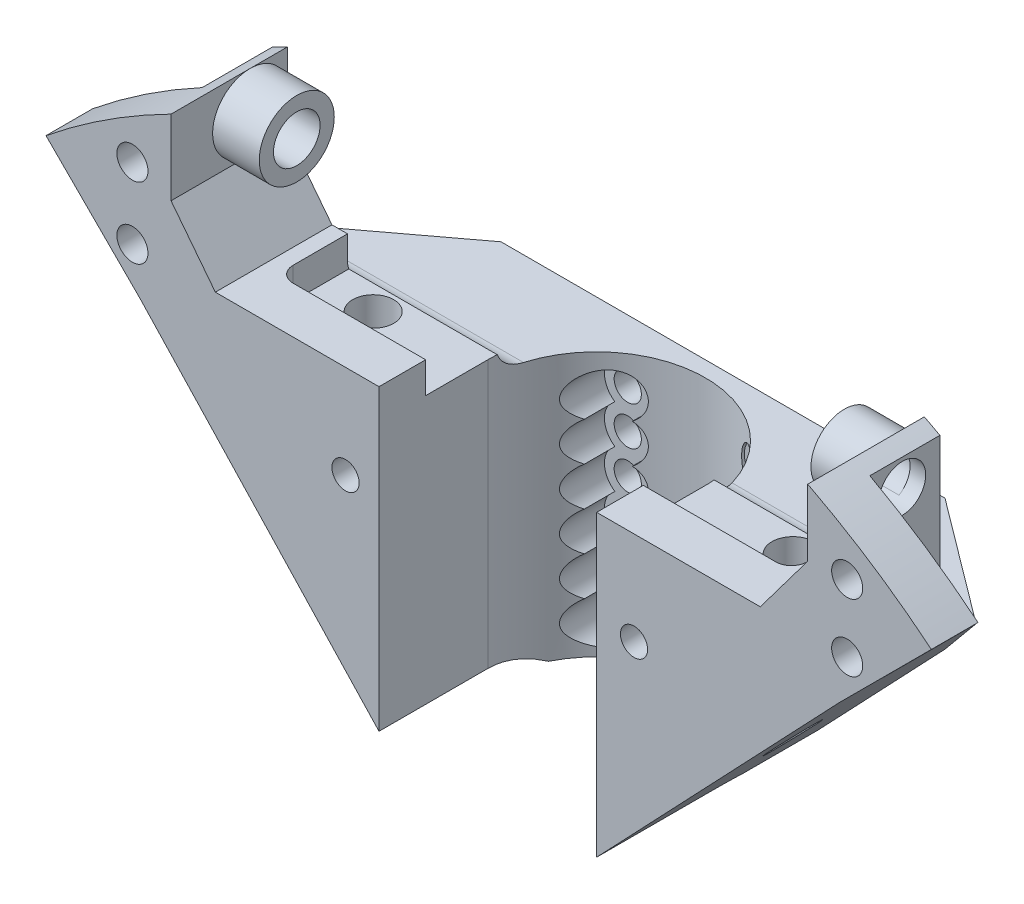
SolidWorks part; units mm, degrees
ref_plane "Front Plane" through (0, 0, 0) normal (0, 0, 1) x (1, 0, 0)
ref_plane "Top Plane" through (0, 0, 0) normal (0, 1, 0) x (1, 0, 0)
ref_plane "Right Plane" through (0, 0, 0) normal (1, 0, 0) x (0, 0, -1)
sketch "Model" plane through (0, 0, 0) normal (0, 0, 1) x (1, 0, 0)
  line L0 (265.571, 46.228) -> (275.731, 56.388)
  line L1 (387.491, 140.716) -> (398.667, 148.844)
  line L2 (349.899, 55.88) -> (359.551, 46.228)
  line L3 (379.871, 94.488) -> (394.603, 85.344)
  line L4 (349.899, 55.88) -> (379.871, 94.488)
  line L5 (358.027, 180.34) -> (369.711, 192.024)
  line L6 (239.155, 141.732) -> (268.111, 180.34)
  line L7 (245.759, 94.488) -> (275.731, 56.388)
  line L8 (227.471, 150.368) -> (239.155, 141.732)
  line L9 (231.027, 84.836) -> (245.759, 94.488)
  line L10 (272.0625, 193.262) -> (272.0625, 202.914)
  line L11 (255.919, 192.532) -> (268.111, 180.34)
  line L12 (353.963, 194.056) -> (353.963, 202.184)
  line L13 (277.763, 185.928) -> (347.867, 185.928)
  line L14 (272.0625, 193.262) -> (277.763, 185.928)
  line L15 (347.867, 185.928) -> (353.963, 194.056)
  line L16 (358.027, 180.34) -> (387.491, 140.716)
  circle A0 centre (288.285, 50.903) radius 0.35
  circle A1 centre (288.285, 47.903) radius 0.35
  circle A2 centre (313.04, 43.867) radius 0.35
  circle A3 centre (313.04, 40.867) radius 0.35
  circle A4 centre (338.328, 47.752) radius 0.35
  circle A5 centre (338.328, 50.752) radius 0.35
  circle A6 centre (388.747, 117.475) radius 0.35
  circle A7 centre (385.747, 117.475) radius 0.35
  circle A8 centre (235.939, 117.475) radius 0.35
  circle A9 centre (238.939, 117.475) radius 0.35
  circle A10 centre (282.458, 118.999) radius 0.35
  circle A11 centre (282.458, 115.999) radius 0.35
  circle A12 centre (289.914, 95.9) radius 0.35
  circle A13 centre (292.914, 95.9) radius 0.35
  circle A14 centre (312.938, 85.446) radius 0.35
  circle A15 centre (312.938, 88.446) radius 0.35
  circle A16 centre (332.915, 95.885) radius 0.35
  circle A17 centre (335.915, 95.885) radius 0.35
  circle A18 centre (343.423, 119.026) radius 0.35
  circle A19 centre (343.423, 116.026) radius 0.35
  circle A20 centre (335.94, 139.075) radius 0.35
  circle A21 centre (332.94, 139.075) radius 0.35
  circle A22 centre (292.916, 138.918) radius 0.35
  circle A23 centre (289.916, 138.918) radius 0.35
  circle A24 centre (337.942, 181.002) radius 0.35
  circle A25 centre (337.942, 178.002) radius 0.35
  circle A26 centre (313.05, 149.379) radius 0.35
  circle A27 centre (313.05, 146.379) radius 0.35
  circle A28 centre (313.558, 171.817) radius 0.35
  circle A29 centre (313.558, 168.817) radius 0.35
  circle A30 centre (286.004, 181.078) radius 0.35
  circle A31 centre (286.004, 178.078) radius 0.35
  circle A32 centre (326.3085, 83.1484) radius 0.55
  circle A33 centre (328.2542, 81.5157) radius 0.55
  circle A34 centre (330.2, 79.883) radius 0.55
  circle A35 centre (332.1457, 78.2503) radius 0.55
  circle A36 centre (334.0915, 76.6176) radius 0.55
  circle A37 centre (336.0373, 74.985) radius 0.55
  circle A38 centre (337.983, 73.3523) radius 0.55
  circle A39 centre (339.9288, 71.7196) radius 0.55
  circle A40 centre (265.571, 46.228) radius 0.125
  circle A41 centre (275.731, 56.388) radius 0.125
  circle A42 centre (387.491, 140.716) radius 0.125
  circle A43 centre (398.667, 148.844) radius 0.125
  circle A44 centre (349.899, 55.88) radius 0.125
  circle A45 centre (359.551, 46.228) radius 0.125
  circle A46 centre (379.871, 94.488) radius 0.125
  circle A47 centre (394.603, 85.344) radius 0.125
  circle A48 centre (349.899, 55.88) radius 0.125
  circle A49 centre (379.871, 94.488) radius 0.125
  circle A50 centre (358.027, 180.34) radius 0.125
  circle A51 centre (369.711, 192.024) radius 0.125
  circle A52 centre (239.155, 141.732) radius 0.125
  circle A53 centre (268.111, 180.34) radius 0.125
  circle A54 centre (245.759, 94.488) radius 0.125
  circle A55 centre (275.731, 56.388) radius 0.125
  circle A56 centre (227.471, 150.368) radius 0.125
  circle A57 centre (239.155, 141.732) radius 0.125
  circle A58 centre (231.027, 84.836) radius 0.125
  circle A59 centre (245.759, 94.488) radius 0.125
  circle A60 centre (272.0625, 193.262) radius 0.2
  circle A61 centre (272.0625, 202.914) radius 0.2
  circle A62 centre (255.919, 192.532) radius 0.125
  circle A63 centre (268.111, 180.34) radius 0.125
  circle A64 centre (353.963, 194.056) radius 0.2
  circle A65 centre (353.963, 202.184) radius 0.2
  circle A66 centre (277.763, 185.928) radius 0.2
  circle A67 centre (347.867, 185.928) radius 0.2
  circle A68 centre (272.0625, 193.262) radius 0.2
  circle A69 centre (277.763, 185.928) radius 0.2
  circle A70 centre (347.867, 185.928) radius 0.2
  circle A71 centre (353.963, 194.056) radius 0.2
  circle A72 centre (358.027, 180.34) radius 0.125
  circle A73 centre (387.491, 140.716) radius 0.125
  circle A74 centre (312.547, 118.364) radius 10
  circle A75 centre (322.547, 118.364) radius 0.125
  circle A76 centre (302.547, 118.364) radius 0.125
  arc A77 (272.0625, 202.914) -> (353.9423, 202.6508) centre (312.7448, 122.6335) ccw
  circle A78 centre (353.9423, 202.6508) radius 0.2
  circle A79 centre (272.0621, 202.9138) radius 0.2
  circle A80 centre (341.009, 84.201) radius 2.5
  circle A81 centre (227.2882, 125.7761) radius 2
  circle A82 centre (227.1612, 118.1561) radius 2
  circle A83 centre (227.711, 110.744) radius 2
  circle A84 centre (227.8719, 133.9959) radius 2
  circle A85 centre (278.0556, 43.4621) radius 2
  circle A86 centre (295.1546, 37.9063) radius 2
  circle A87 centre (330.9154, 37.9063) radius 2
  circle A88 centre (348.0144, 43.4621) radius 2
  circle A89 centre (398.1981, 110.0581) radius 2
  circle A90 centre (399.035, 122.027) radius 2
  circle A91 centre (398.1981, 133.9959) radius 2
  circle A92 centre (395.859, 97.917) radius 2
  circle A93 centre (228.854, 102.997) radius 2
  circle A94 centre (231.013, 94.996) radius 2
  circle A95 centre (271.145, 46.736) radius 2
  circle A96 centre (286.258, 40.386) radius 2
  circle A97 centre (303.911, 36.322) radius 2
  circle A98 centre (322.072, 36.322) radius 2
  circle A99 centre (339.344, 40.386) radius 2
  circle A100 centre (354.076, 47.244) radius 2
  circle A101 centre (393.319, 90.043) radius 2
  circle A102 centre (396.367, 143.256) radius 2
  circle A103 centre (229.235, 144.018) radius 2
  circle A104 centre (313.035, 36.027) radius 2
  circle A105 centre (284.099, 152.527) radius 2.5
  circle A106 centre (272.288, 134.493) radius 2.5
  circle A107 centre (343.027, 152.273) radius 2.5
  circle A108 centre (258.6243, 93.2791) radius 2
  circle A109 centre (324.88, 146.685) radius 2
  circle A110 centre (299.988, 146.685) radius 2
  circle A111 centre (323.864, 177.165) radius 2
  circle A112 centre (301.512, 177.165) radius 2
  circle A113 centre (272.81, 98.425) radius 2.5
  circle A114 centre (352.806, 135.763) radius 2.5
  circle A115 centre (285.6744, 84.5154) radius 2.5
  circle A116 centre (252.871, 143.764) radius 2
  circle A117 centre (355.487, 167.64) radius 2
  circle A118 centre (277.4203, 69.9111) radius 2
  circle A119 centre (348.375, 69.596) radius 2
  circle A120 centre (373.775, 142.748) radius 2
  circle A121 centre (367.171, 93.472) radius 2
  circle A122 centre (270.651, 168.148) radius 2
  circle A123 centre (267.095, 185.928) radius 2
  circle A124 centre (359.043, 185.928) radius 2
  circle A125 centre (352.185, 97.917) radius 2.5
  circle A126 centre (324.88, 152.781) radius 2.5
  circle A127 centre (299.988, 152.781) radius 2.5
  circle A128 centre (323.864, 182.245) radius 2
  circle A129 centre (312.815, 96.52) radius 2
  circle A130 centre (312.815, 101.6) radius 2
  circle A131 centre (359.043, 194.564) radius 2
  circle A132 centre (301.512, 182.245) radius 2
  circle A133 centre (267.095, 195.072) radius 2
  circle A134 centre (312.547, 154.813) radius 1.75
sketch "Sketch2" plane through (0, 0, 0) normal (0, 0, 1) x (1, 0, 0)
  line L0 (369.8693, 192.1806) -> (358.027, 180.34)
  line L1 (255.978, 192.4729) -> (268.111, 180.34)
  line L2 (268.111, 180.34) -> (300.315, 145.928)
  line L3 (353.963, 202.6401) -> (353.963, 194.056)
  line L4 (353.963, 194.056) -> (347.867, 185.928)
  line L5 (347.867, 185.928) -> (277.763, 185.928)
  line L6 (277.763, 185.928) -> (272.0625, 193.262)
  line L7 (272.0625, 193.262) -> (272.0625, 202.914)
  line L8 (300.315, 145.928) -> (325.315, 145.928)
  line L9 (325.315, 145.928) -> (358.027, 180.34)
  line L10 (312.815, 185.928) -> (312.815, 145.928) construction
  arc A0 (272.0625, 202.914) -> (255.978, 192.4729) centre (312.7448, 122.6335) ccw
  arc A1 (272.0625, 202.914) -> (353.9423, 202.6508) centre (312.7448, 122.6335) ccw construction
  arc A3 (369.8693, 192.1806) -> (353.963, 202.6401) centre (312.7448, 122.6335) ccw
  point P11 (0, 0)
  point P13 (0, 0)
  point P31 (369.8693, 192.1806)
  point P32 (0, 0)
  point P33 (369.711, 192.024)
  point P34 (0, 0)
  point P35 (0, 0)
  point P36 (0, 0)
  dimension "D1" = 40
  dimension "D2" = 25
extrude "Boss-Extrude1" add sketch "Sketch2" along normal blind 30
sketch "Sketch3" plane through (0, 185.928, 0) normal (0, 1, 0) x (1, 0, 0)
  line L1 (312.815, -16) -> (312.815, -30) construction
  line L2 (347.867, -30) -> (277.763, -30) construction
  line L3 (326.815, -16) -> (326.815, -30)
  line L4 (326.815, -30) -> (298.815, -30)
  line L5 (298.815, -30) -> (298.815, -16)
  arc A0 (326.815, -16) -> (298.815, -16) centre (312.815, -16) ccw
  dimension "D1" = 28
  dimension "D2" = 14
extrude "Cut-Extrude1" cut sketch "Sketch3" against normal through all
sketch "Sketch4" plane through (0, 0, 0) normal (0, 0, -1) x (-1, 0, 0)
  circle A0 centre (-359.043, 194.564) radius 2
  circle A1 centre (-359.043, 185.928) radius 2
  circle A6 centre (-267.095, 185.928) radius 2
  circle A7 centre (-267.095, 195.072) radius 2
extrude "Cut-Extrude2" cut sketch "Sketch4" against normal through all
sketch "Sketch5" plane through (0, 185.928, 0) normal (0, 1, 0) x (1, 0, 0)
  line L0 (298.815, -30) -> (277.763, -30) construction
  line L1 (281.763, -10) -> (343.867, -10)
  line L2 (279.763, -12) -> (279.763, -22)
  line L3 (281.763, -24) -> (343.867, -24)
  line L4 (345.867, -12) -> (345.867, -22)
  line L5 (277.763, -30) -> (277.763, 0) construction
  line L6 (347.867, -30) -> (347.867, 0) construction
  arc A0 (343.867, -10) -> (345.867, -12) centre (343.867, -12) cw
  arc A1 (343.867, -24) -> (345.867, -22) centre (343.867, -22) ccw
  arc A2 (279.763, -22) -> (281.763, -24) centre (281.763, -22) ccw
  arc A3 (281.763, -10) -> (279.763, -12) centre (281.763, -12) ccw
  dimension "D5" = 2
  dimension "D1" = 6
  dimension "D2" = 14
  dimension "D3" = 2
  dimension "D4" = 2
extrude "Cut-Extrude3" cut sketch "Sketch5" against normal blind 4
sketch "Sketch6" plane through (0, 0, 0) normal (0, 0, -1) x (-1, 0, 0)
  line L1 (-373.8248, 202.914) -> (-252.5793, 202.914)
  line L2 (-373.8248, 202.914) -> (-373.8248, 179.914)
  line L3 (-373.8248, 179.914) -> (-252.5793, 179.914)
  line L4 (-252.5793, 202.914) -> (-252.5793, 179.914)
  dimension "D1" = 23
extrude "Cut-Extrude4" cut sketch "Sketch6" against normal blind 15
sketch "Sketch7" plane through (0, 0, 15) normal (0, 0, -1) x (-1, 0, 0)
  line L0 (-298.8508, 179.914) -> (-268.5097, 179.914) construction
  line L1 (-270.0625, 179.914) -> (-254.227, 179.914)
  line L2 (-270.0625, 179.914) -> (-270.0625, 203.6871)
  line L3 (-270.0625, 203.6871) -> (-254.227, 203.6871)
  line L4 (-254.227, 179.914) -> (-254.227, 203.6871)
  line L5 (-272.0625, 202.914) -> (-272.0625, 193.262) construction
  line L6 (-357.6221, 179.914) -> (-326.7793, 179.914) construction
  line L7 (-355.963, 179.914) -> (-372.7832, 179.914)
  line L8 (-355.963, 179.914) -> (-355.963, 208.3311)
  line L9 (-355.963, 208.3311) -> (-372.7832, 208.3311)
  line L10 (-372.7832, 179.914) -> (-372.7832, 208.3311)
  dimension "D1" = 2
  dimension "D2" = 2
extrude "Cut-Extrude5" cut sketch "Sketch7" against normal blind 9
sketch "Sketch8" plane through (272.0625, 0, 0) normal (1, 0, 0) x (0, 0, -1)
  line L0 (-30, 202.914) -> (-15, 202.914) construction
  line L1 (-15, 202.914) -> (-15, 193.262) construction
  line L2 (-30, 193.262) -> (-15, 193.262) construction
  circle A0 centre (-19.826, 198.088) radius 4.826
  circle A1 centre (-19.826, 198.088) radius 3
  dimension "D1" = 6
extrude "Boss-Extrude2" add sketch "Sketch8" along normal blind 6
sketch "Sketch10" plane through (353.963, 0, 0) normal (-1, 0, 0) x (0, 0, 1)
  line L0 (30, 202.6401) -> (15, 202.6401) construction
  line L1 (30, 194.056) -> (15, 194.056) construction
  line L2 (15, 194.056) -> (15, 202.6401) construction
  circle A0 centre (19.2921, 198.3481) radius 4.2921
  circle A1 centre (19.2921, 198.3481) radius 3
  dimension "D1" = 6
extrude "Boss-Extrude3" add sketch "Sketch10" along normal blind 6
sketch "Sketch9" plane through (272.0625, 0, 0) normal (1, 0, 0) x (0, 0, -1)
  circle A1 centre (-19.826, 198.088) radius 3
  circle A2 centre (-19.826, 198.088) radius 3 construction
extrude "Cut-Extrude6" cut sketch "Sketch9" against normal through all both and the other way through all
sketch "Sketch11" plane through (0, 0, 15) normal (0, 0, -1) x (-1, 0, 0)
  line L1 (-356.109, 187.1425) -> (-358.6278, 189.0762)
  line L2 (-358.6278, 189.0762) -> (-361.5618, 187.8616)
  line L3 (-361.5618, 187.8616) -> (-361.977, 184.7135)
  line L4 (-361.977, 184.7135) -> (-359.4582, 182.7798)
  line L5 (-359.4582, 182.7798) -> (-356.5242, 183.9944)
  line L6 (-356.5242, 183.9944) -> (-356.109, 187.1425)
  line L7 (-356.3436, 192.8917) -> (-356.2451, 196.0656)
  line L8 (-356.2451, 196.0656) -> (-358.9445, 197.7379)
  line L9 (-358.9445, 197.7379) -> (-361.7424, 196.2363)
  line L10 (-361.7424, 196.2363) -> (-361.841, 193.0624)
  line L11 (-361.841, 193.0624) -> (-359.1416, 191.3901)
  line L12 (-359.1416, 191.3901) -> (-356.3436, 192.8917)
  line L13 (-264.9293, 188.2503) -> (-268.0234, 188.9647)
  line L14 (-268.0234, 188.9647) -> (-270.189, 186.6424)
  line L15 (-270.189, 186.6424) -> (-269.2607, 183.6057)
  line L16 (-269.2607, 183.6057) -> (-266.1667, 182.8913)
  line L17 (-266.1667, 182.8913) -> (-264.001, 185.2136)
  line L18 (-264.001, 185.2136) -> (-264.9293, 188.2503)
  line L19 (-264.3228, 193.5234) -> (-264.3678, 196.6986)
  line L20 (-264.3678, 196.6986) -> (-267.1401, 198.2471)
  line L21 (-267.1401, 198.2471) -> (-269.8673, 196.6206)
  line L22 (-269.8673, 196.6206) -> (-269.8222, 193.4454)
  line L23 (-269.8222, 193.4454) -> (-267.05, 191.8969)
  line L24 (-267.05, 191.8969) -> (-264.3228, 193.5234)
  circle A0 centre (-359.043, 185.928) radius 2.75 construction
  circle A1 centre (-359.043, 194.564) radius 2.75 construction
  circle A2 centre (-267.095, 185.928) radius 2.75 construction
  circle A3 centre (-267.095, 195.072) radius 2.75 construction
  dimension "D1" = 5.5
  dimension "D2" = 5.5
  dimension "D3" = 5.5
  dimension "D4" = 5.5
extrude "Cut-Extrude7" cut sketch "Sketch11" against normal blind 2 from surface at -9 starting at face at (269.095, 195.072, 24)
sketch "Sketch12" plane through (0, 179.914, 0) normal (0, 1, 0) x (1, 0, 0)
  line L0 (268.5097, -12) -> (284.5097, 0)
  line L1 (268.5097, -24) -> (268.5097, 0) construction
  line L2 (357.6221, 0) -> (268.5097, 0) construction
  line L3 (357.6221, -12) -> (341.6221, 0)
  line L4 (357.6221, 0) -> (357.6221, -24) construction
  line L5 (284.5097, 0) -> (268.5097, 0)
  line L6 (268.5097, 0) -> (268.5097, -12)
  line L7 (341.6221, 0) -> (357.6221, 0)
  line L8 (357.6221, 0) -> (357.6221, -12)
  dimension "D1" = 16
  dimension "D2" = 16
extrude "Cut-Extrude8" cut sketch "Sketch12" against normal through all
sketch "Sketch13" plane through (0, 0, 0) normal (0, 0, -1) x (-1, 0, 0)
  line L0 (-341.6221, 163.0825) -> (-341.6221, 179.914) construction
  line L1 (-355.963, 179.914) -> (-326.7793, 179.914) construction
  line L2 (-341.6221, 179.914) -> (-284.5097, 179.914) construction
  line L3 (-284.5097, 162.817) -> (-284.5097, 179.914) construction
  circle A0 centre (-331.6221, 173.914) radius 3
  circle A1 centre (-294.5097, 173.914) radius 3
  dimension "D1" = 10
  dimension "D2" = 6
  dimension "D3" = 6
  dimension "D4" = 6
  dimension "D5" = 6
  dimension "D6" = 10
extrude "Cut-Extrude9" cut sketch "Sketch13" against normal blind 25
sketch "Sketch14" plane through (0, 0, 25) normal (0, 0, -1) x (-1, 0, 0)
  circle A0 centre (-331.6221, 173.914) radius 1.75
  circle A1 centre (-294.5097, 173.914) radius 1.75
  dimension "D1" = 3.5
  dimension "D2" = 3.5
extrude "Cut-Extrude10" cut sketch "Sketch14" against normal through all
ref_plane "Plane1" through (0, 0, 3) normal (0, 0, -1) x (-1, 0, 0)
sketch "Sketch16" plane through (0, 0, 3) normal (0, 0, -1) x (-1, 0, 0)
  line L0 (-303.815, 149.928) -> (-321.815, 149.928) construction
  line L1 (-312.815, 149.928) -> (-312.815, 145.928) construction
  line L2 (-325.315, 145.928) -> (-300.315, 145.928) construction
  circle A0 centre (-321.815, 149.928) radius 3
  circle A1 centre (-303.815, 149.928) radius 3
  point P9 (0, 0)
  point P10 (0, 0)
  dimension "D2" = 6
  dimension "D3" = 6
  dimension "D1" = 18
  dimension "D4" = 4
extrude "Cut-Extrude11" cut sketch "Sketch16" against normal through all
sketch "Sketch17" plane through (0, 0, 3) normal (0, 0, 1) x (1, 0, 0)
  line L0 (303.815, 149.928) -> (321.815, 149.928) construction
  line L1 (312.815, 145.928) -> (312.815, 149.928)
  line L2 (300.315, 145.928) -> (325.315, 145.928) construction
  circle A0 centre (303.815, 149.928) radius 1.75
  circle A1 centre (321.815, 149.928) radius 1.75
  dimension "D1" = 3.5
  dimension "D2" = 3.5
  dimension "D3" = 18
  dimension "D4" = 4
extrude "Cut-Extrude12" cut sketch "Sketch17" against normal through all from surface at 0 starting at face at (300.815, 149.928, 3)
pattern_linear "LPattern1" count 6 spacing 5 along (0, 1, 0) of "Cut-Extrude11", "Cut-Extrude12"
fillet "Fillet1" radius 3 2 edges at (341.3711, 179.914, 15) (284.4566, 179.914, 15)
sketch "Sketch18" plane through (0, 181.928, 0) normal (0, 1, 0) x (1, 0, 0)
  line L0 (286.0659, -18) -> (340.0659, -18) construction
  line L1 (313.0659, 0) -> (313.0659, -18) construction
  line L2 (341.6221, 0) -> (284.5097, 0) construction
  circle A0 centre (286.0659, -18) radius 2.6431
  circle A1 centre (340.0659, -18) radius 2.7138
  dimension "D1" = 54
  dimension "D2" = 18
extrude "Cut-Extrude13" cut sketch "Sketch18" against normal through all
